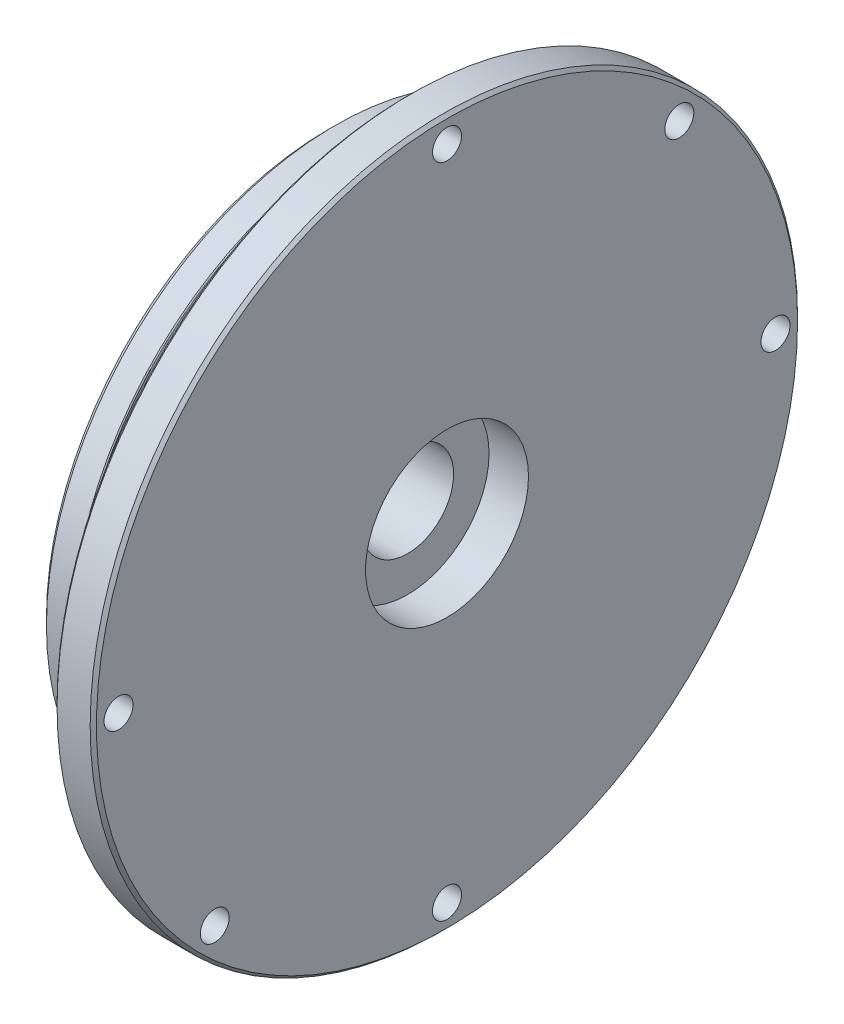
SolidWorks part; units mm, degrees
ref_plane "Front Plane" through (0, 0, 0) normal (0, 0, 1) x (1, 0, 0)
ref_plane "Top Plane" through (0, 0, 0) normal (0, 1, 0) x (1, 0, 0)
ref_plane "Right Plane" through (0, 0, 0) normal (1, 0, 0) x (0, 0, -1)
ref_plane "Plane1" through (0, 0, 0) normal (0, 0, -1) x (-1, 0, 0)
sketch "Sketch1" plane through (0, 0, 0) normal (0, 0, -1) x (-1, 0, 0)
  line L0 (-14.2875, 42.7355) -> (-14.2875, 0)
  line L1 (-14.2875, 0) -> (0, 0)
  line L2 (0, 0) -> (0, 34.8996)
  line L3 (0, 34.8996) -> (-3.937, 34.8996)
  line L4 (-3.937, 34.8996) -> (-3.937, 33.655)
  line L5 (-3.937, 33.655) -> (-6.35, 33.655)
  line L6 (-6.35, 33.655) -> (-6.35, 34.8996)
  line L7 (-6.35, 34.8996) -> (-9.525, 34.8996)
  line L8 (-9.525, 34.8996) -> (-9.525, 42.7355)
  line L9 (-9.525, 42.7355) -> (-14.2875, 42.7355)
  line L10 (-14.2875, 0) -> (0, 0) construction
revolve "Revolve1" add sketch "Sketch1" angle 360 about L10
hole_wizard "M3 Clearance Hole1" positions "Sketch3" profile "Sketch2" hole size "M3" standard "ANSI Metric"
sketch "Sketch3" plane through (9.525, 0, 0) normal (-1, 0, 0) x (0, 0, 1)
  point P0 (28.0633, -28.0633)
  point P1 (-28.0633, 28.0633)
  point P2 (39.6875, 0)
  point P3 (-39.6875, 0)
  point P4 (0, -39.6875)
  point P5 (0, 39.6875)
sketch "Sketch2" plane through (9.525, -28.0633, 28.0633) normal (0, 1, 0) x (0, 0, 1)
  line L0 (0, 0) -> (0, 4.7625)
  line L1 (0, 4.7625) -> (1.7526, 4.7625)
  line L2 (1.7526, 4.7625) -> (1.7526, 0)
  line L5 (1.7526, 0) -> (0, 0)
  line L11 (0, -6.35) -> (0, 107.95) construction
  dimension "Thru Hole Dia." = 3.5052
  dimension "Thru Hole Depth" = 4.7625
hole_wizard "CBORE for M10 Hex Head Bolt1" positions "Sketch5" profile "Sketch4" counterbore size "M10" standard "ANSI Metric"
sketch "Sketch5" plane through (14.2875, 0, 0) normal (1, 0, 0) x (0, 0, -1)
  point P0 (0, 0)
sketch "Sketch4" plane through (14.2875, 0, 0) normal (0, 1, 0) x (0, 0, -1)
  line L0 (0, 0) -> (0, 14.2875)
  line L1 (0, 14.2875) -> (5.5563, 14.2875)
  line L3 (5.5563, 14.2875) -> (5.5563, 4.7625)
  line L4 (5.5563, 4.7625) -> (9.8425, 4.7625)
  line L5 (9.8425, 4.7625) -> (9.8425, 0)
  line L7 (9.8425, 0) -> (0, 0)
  line L11 (0, -6.35) -> (0, 107.95) construction
  dimension "Thru Hole Dia." = 11.1125
  dimension "Thru Hole Depth" = 14.2875
  dimension "C'Bore Dia." = 19.685
  dimension "C'Bore Depth" = 4.7625
chamfer "Chamfer1" distance 0.381 angle 45 2 edges at (14.2875, 0, 42.7355) (9.525, 0, 42.7355)
chamfer "Chamfer2" distance 0.7874 angle 45 1 edges at (0, 0, 34.8996)
fillet "Fillet1" radius 0.127 2 edges at (6.35, 0, 34.8996) (3.937, 0, 34.8996)
fillet "Fillet2" radius 0.381 2 edges at (6.35, 0, 33.655) (3.937, 0, 33.655)
